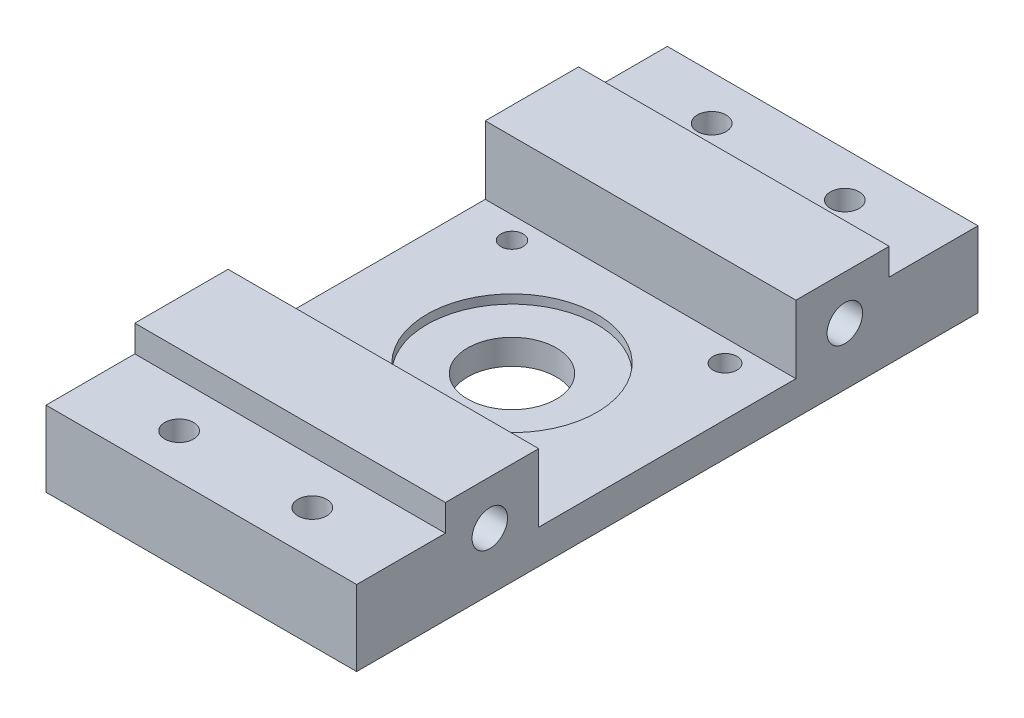
SolidWorks part; units mm, degrees
ref_plane "Front Plane" through (0, 0, 0) normal (0, 0, 1) x (1, 0, 0)
ref_plane "Top Plane" through (0, 0, 0) normal (0, 1, 0) x (1, 0, 0)
ref_plane "Right Plane" through (0, 0, 0) normal (1, 0, 0) x (0, 0, -1)
sketch "Sketch12" plane through (0, 0, 0) normal (1, 0, 0) x (0, 0, -1)
  line L0 (71.7005, 0) -> (-73.3454, 0) construction
  line L1 (70.0054, 14) -> (70.0054, -11.771) construction
  line L3 (70.0054, -3) -> (-70, -3)
  line L4 (70.0054, -3) -> (70.0054, 14)
  line L5 (50, 20) -> (-50, 20)
  line L6 (-70, -3) -> (-70, 14)
  line L8 (162.5, -3) -> (-162.5, -3) construction
  line L9 (50, 20) -> (-50, 20) construction
  line L10 (70.0054, 14) -> (50, 14)
  line L11 (50, 14) -> (50, 20)
  line L12 (-70, 14) -> (-50, 14)
  line L13 (-50, 14) -> (-50, 20)
extrude "Boss-Extrude1" add sketch "Sketch12" along normal blind 70
sketch "Sketch14" plane through (0, 0, 0) normal (-1, 0, 0) x (0, 0, 1)
  line L0 (0, 20) -> (0, 0) construction
  line L4 (-40, 10) -> (40, 10) construction
  line L5 (-50, 20) -> (50, 20) construction
  circle A0 centre (-40, 10) radius 4
  circle A1 centre (40, 10) radius 4
  point P4 (0, 10)
  point P5 (0, 10)
  dimension "D2" = 8
  dimension "D3" = 8
  dimension "D1" = 80
extrude "Cut-Extrude1" cut sketch "Sketch14" against normal up to next
sketch "Sketch15" plane through (0, 14, 0) normal (0, 1, 0) x (1, 0, 0)
  line L0 (70, 60.0027) -> (0, 60.0027) construction
  line L1 (70, 70.0054) -> (70, 50) construction
  line L2 (0, 70.0054) -> (0, 50) construction
  line L3 (70, -60) -> (0, -60) construction
  line L5 (70, -50) -> (70, -70) construction
  line L6 (0, -50) -> (0, -70) construction
  circle A0 centre (50, 60.0027) radius 3.25
  circle A1 centre (20, 60.0027) radius 3.25
  circle A2 centre (50, -60) radius 3.25
  circle A3 centre (20, -60) radius 3.25
  dimension "D1" = 6.5
  dimension "D2" = 6.5
  dimension "D3" = 6.5
  dimension "D4" = 6.5
  dimension "D5" = 20
  dimension "D6" = 20
  dimension "D7" = 20
  dimension "D8" = 20
extrude "Cut-Extrude2" cut sketch "Sketch15" against normal up to next
sketch "Sketch16" plane through (0, 0, 0) normal (-1, 0, 0) x (0, 0, 1)
  line L0 (0, 20) -> (0, -3) construction
  line L1 (-50, 20) -> (50, 20) construction
  line L2 (-162.5, -3) -> (162.5, -3) construction
  line L4 (-28.9755, 21.3504) -> (28.9755, 21.3504)
  line L5 (-28.9755, 21.3504) -> (-28.9755, 4.6722)
  line L6 (-28.9755, 4.6722) -> (28.9755, 4.6722)
  line L7 (28.9755, 21.3504) -> (28.9755, 4.6722)
  line L8 (-28.9755, 21.3504) -> (28.9755, 4.6722) construction
  line L9 (-28.9755, 4.6722) -> (28.9755, 21.3504) construction
  point P6 (0, 13.0113)
extrude "Cut-Extrude3" cut sketch "Sketch16" against normal up to next
sketch "Sketch17" plane through (0, 4.6722, 0) normal (0, 1, 0) x (1, 0, 0)
  line L0 (0, 0) -> (70, 0) construction
  line L5 (70, 28.9755) -> (70, -28.9755) construction
  circle A0 centre (35, 0) radius 19.15
  dimension "D1" = 38.3
extrude "Cut-Extrude4" cut sketch "Sketch17" against normal blind 2
sketch "Sketch18" plane through (0, 2.6722, 0) normal (0, 1, 0) x (1, 0, 0)
  circle A0 centre (35, 0) radius 10
  dimension "D1" = 20
extrude "Cut-Extrude5" cut sketch "Sketch18" against normal up to next
sketch "Sketch19" plane through (0, 4.6722, 0) normal (0, 1, 0) x (1, 0, 0)
  circle A0 centre (11, 24) radius 2.5
  circle A1 centre (59, 24) radius 2.7
  circle A2 centre (59, -24) radius 2.6185
  circle A3 centre (11, -24) radius 2.7
extrude "Cut-Extrude6" cut sketch "Sketch19" against normal up to next
